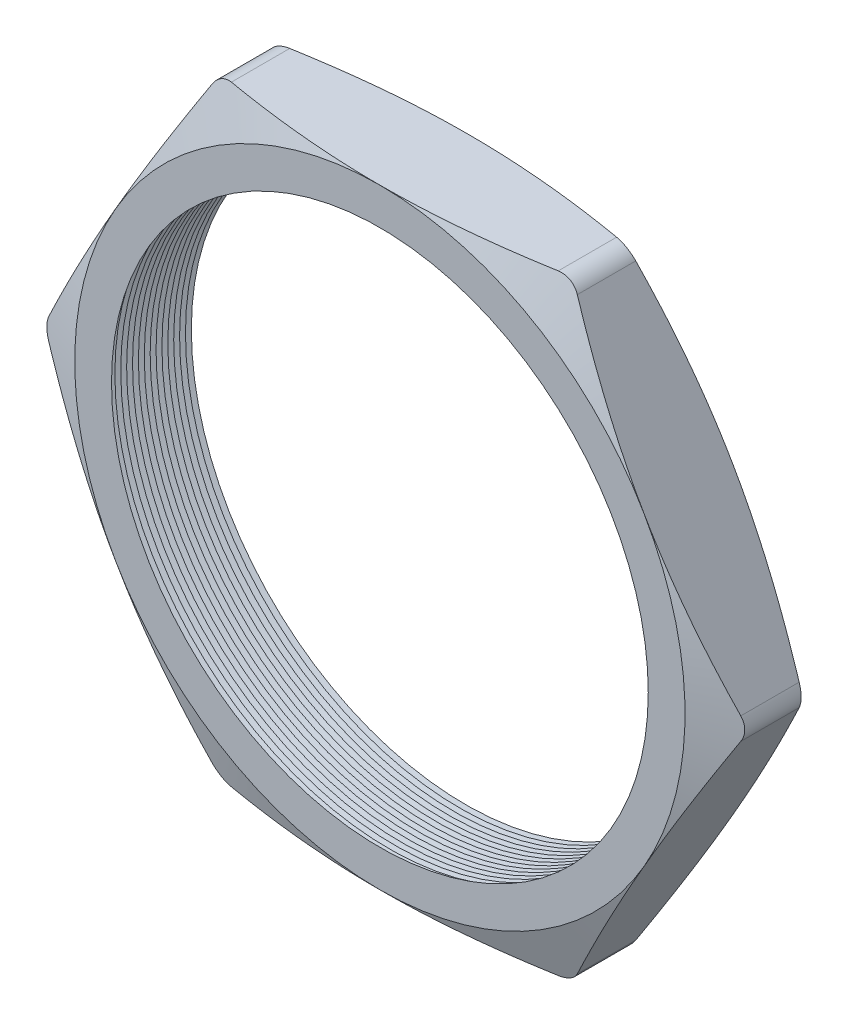
SolidWorks part; units mm, degrees
ref_plane "Front Plane" through (0, 0, 0) normal (0, 0, 1) x (1, 0, 0)
ref_plane "Top Plane" through (0, 0, 0) normal (0, 1, 0) x (1, 0, 0)
ref_plane "Right Plane" through (0, 0, 0) normal (1, 0, 0) x (0, 0, -1)
sketch "Sketch1" plane through (0, 0, 0) normal (0, 0, 1) x (1, 0, 0)
  line L1 (-12.1717, 0) -> (-6.0858, -10.541)
  line L2 (-6.0858, -10.541) -> (6.0858, -10.541)
  line L3 (6.0858, -10.541) -> (12.1717, 0)
  line L4 (12.1717, 0) -> (6.0858, 10.541)
  line L5 (6.0858, 10.541) -> (-6.0858, 10.541)
  line L6 (-6.0858, 10.541) -> (-12.1717, 0)
  circle A0 centre (0, 0) radius 10.541 construction
  circle A1 centre (0, 0) radius 9.271
  dimension "TS" = 18.542
  dimension "H" = 21.082
extrude "Extrude1" add sketch "Sketch1" along normal blind 3.048
fillet "Fillet1" radius 0.762 6 edges at (-6.0858, 10.541, 1.524) (-12.1717, 0, 1.524) (-6.0858, -10.541, 1.524) (6.0858, -10.541, 1.524) (12.1717, 0, 1.524) (6.0858, 10.541, 1.524)
sketch "Sketch2" plane through (0, 0, 3.048) normal (0, 0, 1) x (1, 0, 0)
  line L0 (5.6459, 10.541) -> (-5.6459, 10.541) construction
  circle A0 centre (0, 0) radius 10.541
extrude "Cut-Extrude1" cut sketch "Sketch2" against normal through all draft 70 flip side to cut
sketch "Sketch3" plane through (0, 0, 0) normal (0, 0, -1) x (-1, 0, 0)
  circle A0 centre (0, 0) radius 10.541
extrude "Cut-Extrude2" cut sketch "Sketch3" against normal through all draft 70 flip side to cut
sketch "Sketch4" plane through (0, 0, 0) normal (0, 1, 0) x (1, 0, 0)
  line L0 (-9.271, -3.048) -> (-9.271, -2.6081)
  line L2 (-9.271, -2.6081) -> (-9.652, -2.828)
  line L3 (-9.652, -2.828) -> (-9.271, -3.048)
  line L5 (-9.271, 0) -> (-9.271, -3.048) construction
  line L6 (-9.271, -3.048) -> (9.271, -3.048) construction
  dimension "D1" = 60
  dimension "D2" = 60
  dimension "D3" = 0.381
revolve "Cut-Revolve1" cut sketch "Sketch4" angle 360 about axis through (0, 0, 3.048) along (0, 0, -1)
pattern_linear "LPattern1" count 15 spacing 0.2032 along (0, 0, -1) of "Cut-Revolve1"
